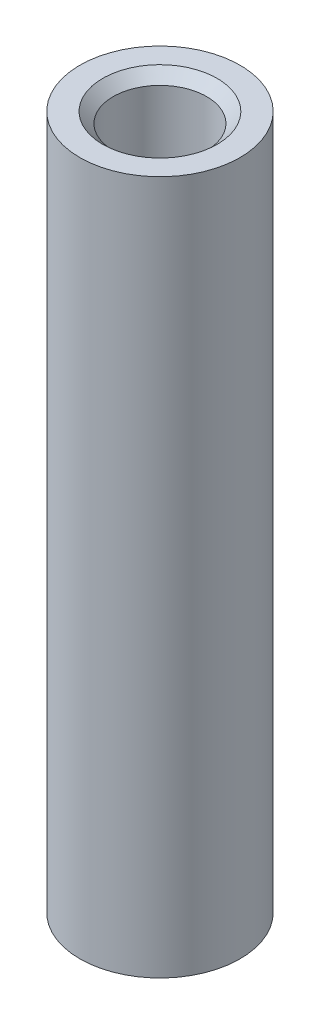
SolidWorks part; units mm, degrees
material "Natural Rubber"
ref_plane "Front Plane" through (0, 0, 0) normal (0, 0, 1) x (1, 0, 0)
ref_plane "Top Plane" through (0, 0, 0) normal (0, 1, 0) x (1, 0, 0)
ref_plane "Right Plane" through (0, 0, 0) normal (1, 0, 0) x (0, 0, -1)
sketch "Sketch1" plane through (0, 0, 0) normal (0, 1, 0) x (1, 0, 0)
  circle A0 centre (0, 0) radius 38.1
  circle A1 centre (0, 0) radius 22.225
  dimension "D1" = 76.2
  dimension "D2" = 44.45
extrude "Boss-Extrude1" add sketch "Sketch1" along normal blind 330.2
chamfer "Chamfer2" distance 5 angle 45 1 edges at (0, 330.2, 22.225)
